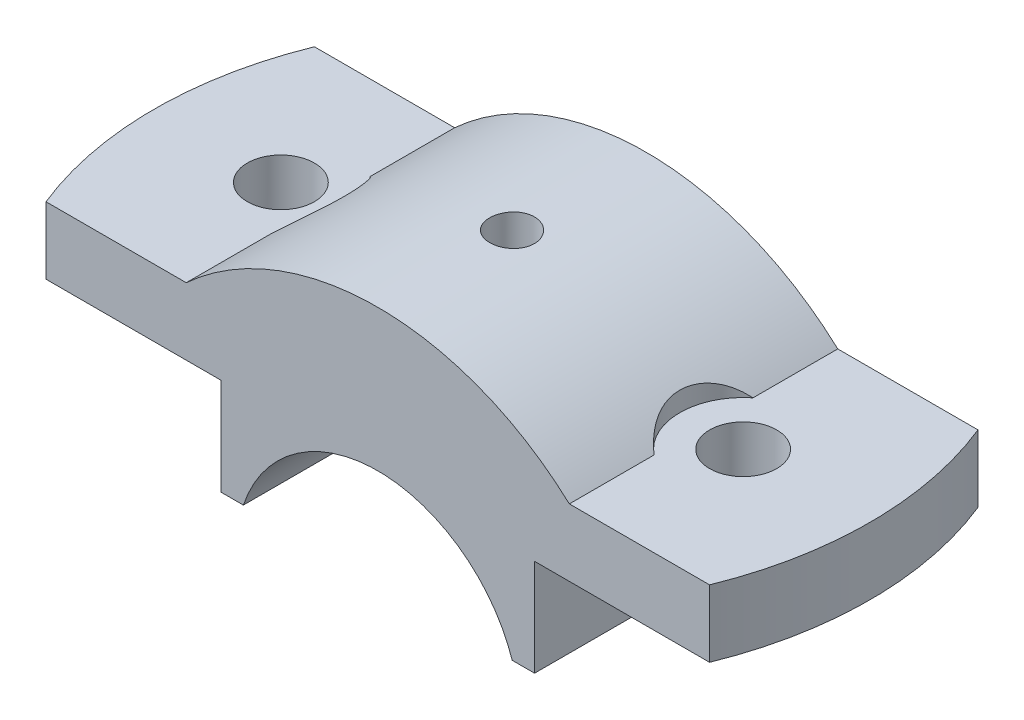
SolidWorks part; units mm, degrees
ref_plane "Front Plane" through (0, 0, 0) normal (0, 0, 1) x (1, 0, 0)
ref_plane "Top Plane" through (0, 0, 0) normal (0, 1, 0) x (1, 0, 0)
ref_plane "Right Plane" through (0, 0, 0) normal (1, 0, 0) x (0, 0, -1)
sketch "Sketch1" plane through (0, 0, 0) normal (0, 0, 1) x (1, 0, 0)
  line L0 (18.0278, 6) -> (21.0278, 6)
  line L1 (21.0278, 6) -> (21.0278, 19)
  line L2 (21.0278, 19) -> (50, 19)
  line L3 (50, 19) -> (50, 28)
  line L4 (50, 28) -> (25.6905, 28)
  line L6 (0, 0) -> (0, 65.7095) construction
  line L7 (-18.0278, 6) -> (-21.0278, 6)
  line L8 (-21.0278, 6) -> (-21.0278, 19)
  line L10 (-21.0278, 19) -> (-50, 19)
  line L11 (-50, 19) -> (-50, 28)
  line L12 (-50, 28) -> (-25.6905, 28)
  arc A0 (18.0278, 6) -> (-18.0278, 6) centre (0, 0) ccw
  arc A1 (25.6905, 28) -> (-25.6905, 28) centre (0, 0) ccw
  dimension "D1" = 38
  dimension "D2" = 76
  dimension "D3" = 6
  dimension "D4" = 3
  dimension "D5" = 13
  dimension "D6" = 9
  dimension "D7" = 50
extrude "Boss-Extrude2" add sketch "Sketch1" along normal mid plane 36 contours A1 L12 L11 L10 L8 L7 A0 L0 L1 L2 L3 L4
hole_wizard "Ø6.0mm Dowel Hole4" positions "Sketch13" profile "Sketch14" hole size "Ø6.0" standard "ANSI Metric" end condition through all
sketch "Sketch13" plane through (0, 28, 0) normal (0, 1, 0) x (1, 0, 0)
  point P0 (-31, 0)
  dimension "D1" = 31
sketch "Sketch14" plane through (-31, 28, 0) normal (1, 0, 0) x (0, 0, 1)
  line L0 (0, 0) -> (0, 22)
  line L1 (0, 22) -> (4.5, 22)
  line L2 (4.5, 22) -> (4.5, 0)
  line L5 (4.5, 0) -> (0, 0)
  line L11 (0, -6.35) -> (0, 107.95) construction
  dimension "Thru Hole Dia." = 9
  dimension "Thru Hole Depth" = 22
mirror "Mirror1" about plane through (0, 0, 0) normal (1, 0, 0) of "Ø6.0mm Dowel Hole4"
ref_plane "Plane2" through (0, 38, 0) normal (0, 1, 0) x (1, 0, 0)
sketch "Sketch16" plane through (0, 38, 0) normal (0, 1, 0) x (1, 0, 0)
  circle A0 centre (-31, 0) radius 8.5
  dimension "D1" = 17
extrude "Cut-Extrude1" cut sketch "Sketch16" against normal up to surface (10 mm away) up to face at (-31, 28, 4.5)
sketch "Sketch17" plane through (0, 28, 0) normal (0, 1, 0) x (1, 0, 0)
  circle A0 centre (31, 0) radius 8.5
  dimension "D1" = 17
extrude "Cut-Extrude2" cut sketch "Sketch17" along normal blind 45
hole_wizard "CBORE for M5 Hex Head Bolt1" positions "3DSketch8" profile "Sketch18" counterbore size "M5" standard "ANSI Metric" end condition through all
sketch3d "3DSketch8"
  point P0 (0, 38, 0)
  dimension "D1" = 0
  dimension "D2" = 0
sketch "Sketch18" plane through (0, 38, 0) normal (1, 0, 0) x (0, 0, 1)
  line L0 (0, 0) -> (0, 32)
  line L1 (0, 32) -> (2.5, 32)
  line L2 (2.5, 13.495) -> (2.5, 32)
  line L3 (2.5, 13.495) -> (2.995, 13)
  line L4 (2.995, 13) -> (3, 13)
  line L5 (3, 13) -> (3, 0)
  line L7 (0, 0) -> (3, 0)
  line L9 (-2.5, 13.495) -> (-2.995, 13) construction
  line L11 (0, -6.35) -> (0, 107.95) construction
  dimension "Thru Hole Dia." = 5
  dimension "Thru Hole Depth" = 32
  dimension "C'Bore Dia." = 6
  dimension "C'Bore Depth" = 13
  dimension "Mid C'Sink Dia." = 5.99
  dimension "Mid C'Sink Angle" = 90
sketch "Sketch19" plane through (0, 28, 0) normal (0, 1, 0) x (1, 0, 0)
  line L0 (-50, 18) -> (-25.6905, 18) construction
  line L1 (-50, -18) -> (-50, 18) construction
  line L2 (-50, -18) -> (-25.6905, -18) construction
  line L3 (-50, 18) -> (-44.4972, 18)
  line L4 (-50, -18) -> (-50, 18)
  line L5 (-50, -18) -> (-44.4972, -18)
  arc A0 (-44.4972, 18) -> (-44.4972, -18) centre (0, 0) ccw
  dimension "D1" = 48
extrude "Cut-Extrude3" cut sketch "Sketch19" against normal through all
mirror "Mirror2" about plane through (0, 0, 0) normal (1, 0, 0) of "Cut-Extrude3"
